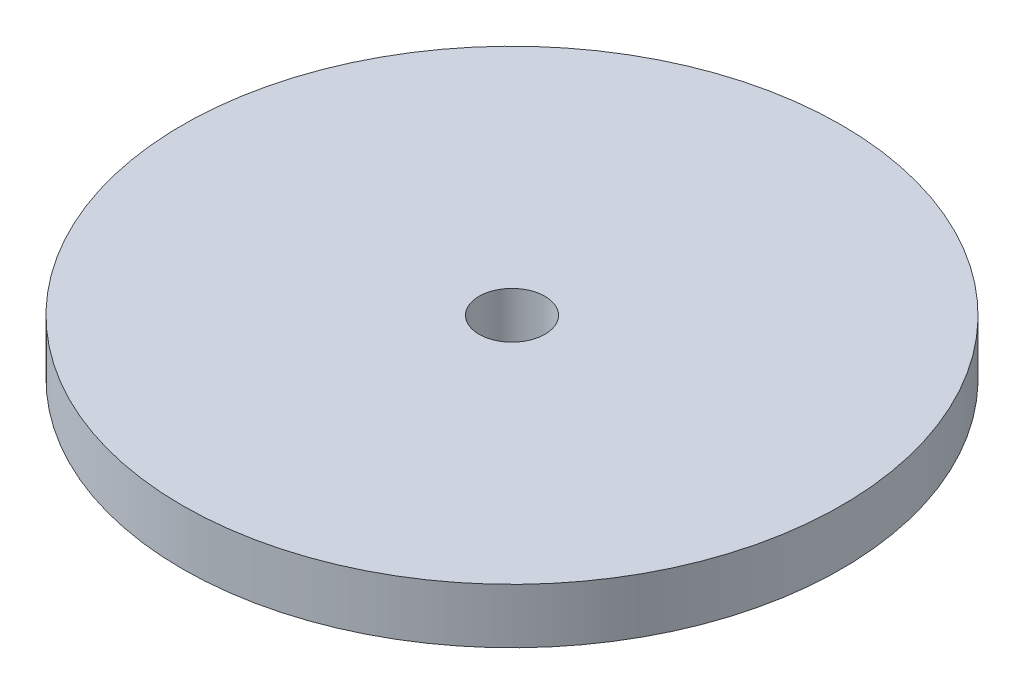
SolidWorks part; units mm, degrees
ref_plane "Front Plane" through (0, 0, 0) normal (0, 0, 1) x (1, 0, 0)
ref_plane "Top Plane" through (0, 0, 0) normal (0, 1, 0) x (1, 0, 0)
ref_plane "Right Plane" through (0, 0, 0) normal (1, 0, 0) x (0, 0, -1)
sketch "Sketch1" plane through (0, 0, 0) normal (0, 1, 0) x (1, 0, 0)
  circle A0 centre (0, 0) radius 3
  circle A1 centre (0, 0) radius 30
extrude "Boss-Extrude1" add sketch "Sketch1" along normal blind 5
